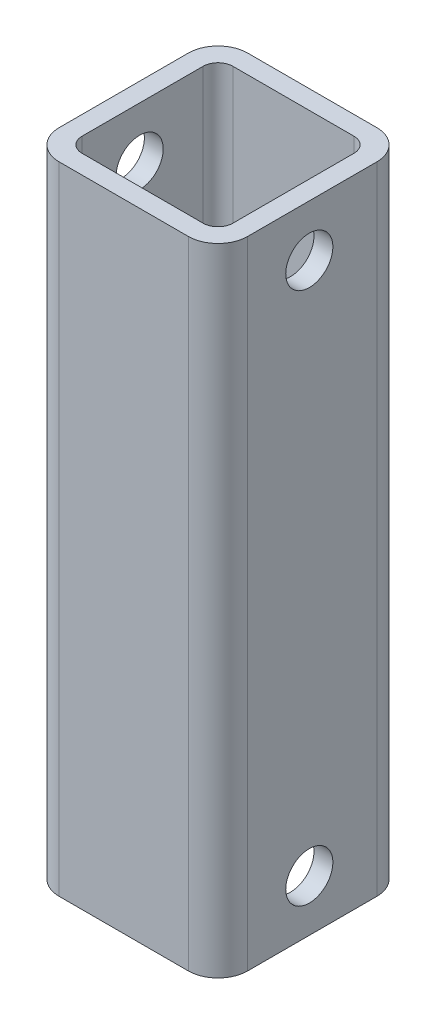
SolidWorks part; units mm, degrees
ref_plane "Front Plane" through (0, 0, 0) normal (0, 0, 1) x (1, 0, 0)
ref_plane "Top Plane" through (0, 0, 0) normal (0, 1, 0) x (1, 0, 0)
ref_plane "Right Plane" through (0, 0, 0) normal (1, 0, 0) x (0, 0, -1)
sketch "Sketch1" plane through (0, 0, 0) normal (0, 1, 0) x (1, 0, 0)
  line L1 (4, 0) -> (21.4, 0)
  line L2 (0, 4) -> (0, 21.4)
  line L3 (4, 25.4) -> (21.4, 25.4)
  line L4 (25.4, 4) -> (25.4, 21.4)
  line L6 (20.86, 2.54) -> (4.54, 2.54)
  line L7 (22.86, 4.54) -> (22.86, 20.86)
  line L8 (2.54, 4.54) -> (2.54, 20.86)
  line L9 (20.86, 22.86) -> (4.54, 22.86)
  line L10 (22.86, 2.54) -> (2.54, 22.86) construction
  line L11 (2.54, 2.54) -> (22.86, 22.86) construction
  arc A0 (2.54, 20.86) -> (4.54, 22.86) centre (4.54, 20.86) cw
  arc A1 (22.86, 20.86) -> (20.86, 22.86) centre (20.86, 20.86) ccw
  arc A2 (22.86, 4.54) -> (20.86, 2.54) centre (20.86, 4.54) cw
  arc A3 (4.54, 2.54) -> (2.54, 4.54) centre (4.54, 4.54) cw
  arc A4 (0, 21.4) -> (4, 25.4) centre (4, 21.4) cw
  arc A5 (21.4, 25.4) -> (25.4, 21.4) centre (21.4, 21.4) cw
  arc A6 (21.4, 0) -> (25.4, 4) centre (21.4, 4) ccw
  arc A7 (4, 0) -> (0, 4) centre (4, 4) cw
  point P9 (12.7, 12.7)
  point P31 (0, 0)
  dimension "D1" = 2
  dimension "D2" = 2
  dimension "D3" = 4
  dimension "D4" = 4
  dimension "D5" = 4
  dimension "D6" = 4
extrude "Boss-Extrude1" add sketch "Sketch1" along normal up to surface (85.725 mm away)
sketch "Sketch2" plane through (25.4, 0, 0) normal (1, 0, 0) x (0, 0, -1)
  circle A0 centre (12.3031, 6.9453) radius 3.175
  circle A1 centre (12.3031, 78.7797) radius 3.175
extrude "Cut-Extrude1" cut sketch "Sketch2" against normal through all both and the other way through all
